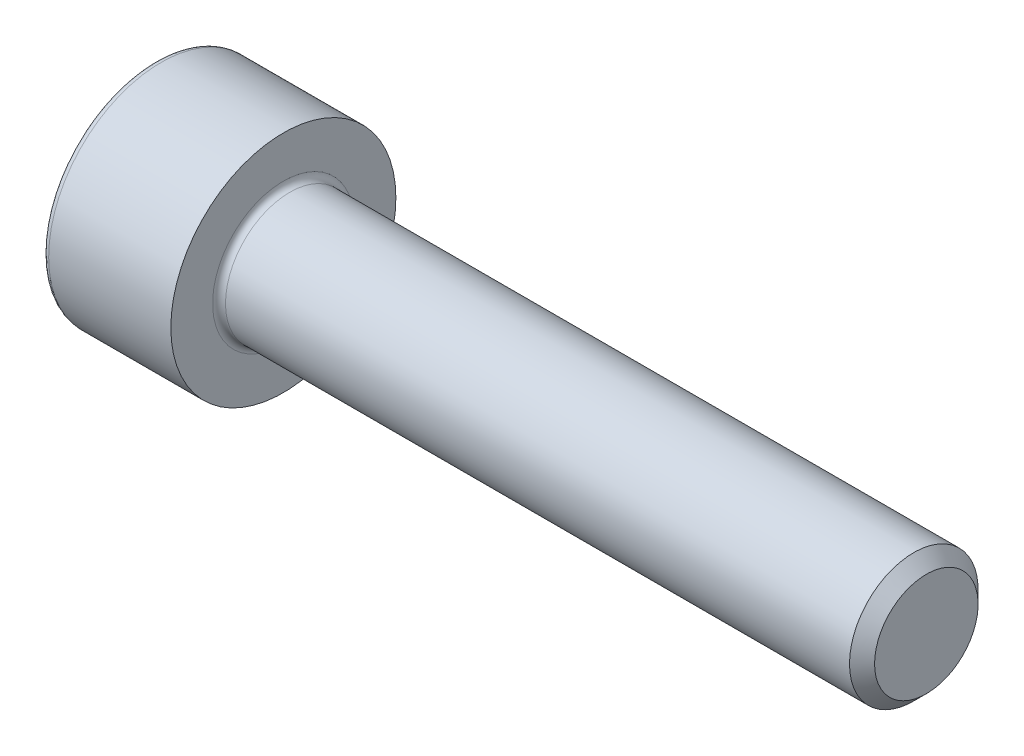
SolidWorks part; units mm, degrees
revolve "Base-Revolve" add sketch "BodySke"
sketch "BodySke" plane through (0, 0, 0) normal (0, 0, 1) x (1, 0, 0)
  line L0 (0, 0) -> (0, 3.5)
  line L1 (0, 3.5) -> (4, 3.5)
  line L2 (4, 3.5) -> (4, 2)
  line L3 (4, 2) -> (23.61, 2)
  line L4 (24, 1.61) -> (24, 0)
  line L5 (24, 0) -> (0, 0)
  line L6 (-31.75, 0) -> (127, 0) construction
  line L8 (24, 1.61) -> (23.61, 2)
  line L10 (24, -1.61) -> (23.61, -2) construction
  line L11 (4.7, 9.525) -> (4.7, 3.175) construction
  line L12 (18, 9.525) -> (18, 3.175) construction
  line L13 (-36, 9.525) -> (-36, 3.175) construction
  dimension "Head_ht" = 4
  dimension "Length" = 20
  dimension "Body_ch_ang" = 45
  dimension "Diameter" = 4
  dimension "Minor_dia" = 3.22
  dimension "Advance" = 0.7
  dimension "Thread_nom" = 6
  dimension "Thread_length" = 60
  dimension "Head_dia" = 7
cosmetic thread "ThreadCosmetic" [suppressed]
fillet "Fillet1" radius 0.2 1 edges at (4, 0, 2)
fillet "Fillet2" radius 0.2 1 edges at (0, 0, 3.5)
ref_plane "Plane1" through (0, 0, 0) normal (0, 0, 1) x (1, 0, 0)
ref_plane "Plane2" through (0, 0, 0) normal (0, 1, 0) x (1, 0, 0)
ref_plane "Plane3" through (0, 0, 0) normal (1, 0, 0) x (0, 0, -1)
sketch "Sketch2" plane through (0, 0, 0) normal (0, 0, 1) x (1, 0, 0)
  line L0 (0, 1.5355) -> (2, 1.5355)
  line L1 (2, 1.5355) -> (2.8865, 0)
  line L2 (-31.75, 0) -> (127, 0) construction
  line L3 (2.8865, 0) -> (0, 0)
  line L4 (0, 0) -> (0, 1.5355)
  line L6 (0, 0) -> (47.625, 0) construction
  dimension "D1" = 1.5355
  dimension "D2" = 60
  dimension "Depth" = 2
revolve "Hex-PreBroach" cut sketch "Sketch2" angle 360 about L6
sketch "Sketch3" plane through (0, 0, 0) normal (-1, 0, 0) x (0, 0.5, 0.866)
  line L0 (0.8865, 1.5355) -> (-0.8865, 1.5355)
  line L1 (-0.8865, 1.5355) -> (-1.773, 0)
  line L2 (0.8865, 1.5355) -> (1.773, 0)
  line L3 (0.8865, -1.5355) -> (1.773, 0)
  line L4 (0.8865, -1.5355) -> (-0.8865, -1.5355)
  line L5 (-0.8865, -1.5355) -> (-1.773, 0)
  dimension "D1" = 1.5355
  dimension "D2" = 1.5355
  dimension "Hex_size" = 3.071
extrude "Hex" cut sketch "Sketch3" against normal blind 2
sketch "ThdSchSke" plane through (0, 0, 0) normal (0, 0, 1) x (1, 0, 0)
  line L0 (18, -1.61) -> (17.7269, -2)
  line L1 (18, -1.61) -> (18.2731, -2)
  line L2 (18.2731, -2) -> (18.2731, -2.5)
  line L3 (-3.175, 0) -> (5.1513, 0) construction
  line L4 (0, 3.3) -> (0, -3.3) construction
  line L5 (18.2731, -2.5) -> (17.7269, -2.5)
  line L6 (17.7269, -2.5) -> (17.7269, -2)
  dimension "Thread_minor" = 3.22
  dimension "Diameter" = 4
  dimension "Start" = 18
revolve "ThreadSchematic" [suppressed] cut sketch "ThdSchSke" angle 360 about L3
pattern_linear "ThdSchPat" [suppressed]
equation "\"D2@Sketch3\" = \"Hex_size@Sketch3\" / 2"
equation "\"D1@Sketch3\" = \"Hex_size@Sketch3\" / 2"
equation "\"D1@Sketch2\" = \"Hex_size@Sketch3\" / 2"
equation "\"Thread_minor@ThreadCosmetic\"  =  \"Minor_dia@BodySke\""
equation "\"Depth@Sketch2\" =  \"Key_eng@Hex\""
equation "\"Thread_length@ThreadCosmetic\" = ((sgn( (\"Length@BodySke\" - \"Advance@BodySke\" * 3.0) - \"Thread_nom@BodySke\" )-1)*( (\"Length@BodySke\" - \"Advance@BodySke\" * 3.0) - \"Thread_nom@BodySke\" ))/-2+ \"Thread_nom@BodySke\""
equation "\"Thread_minor@ThdSchSke\" = \"Minor_dia@BodySke\""
equation "\"Diameter@ThdSchSke\" = \"Diameter@BodySke\""
equation "\"Overcut@ThdSchSke\" = \"Diameter@BodySke\" * 1.25"
equation "\"Start@ThdSchSke\" = \"Head_ht@BodySke\" + \"Length@BodySke\" - \"Thread_length@ThreadCosmetic\"  '---Non-countersunk---"
equation "\"Num_threads@ThdSchPat\" = int( \"Thread_length@ThreadCosmetic\" / \"Advance@BodySke\" + 0.999 )  + 1"
equation "\"Advance@ThdSchPat\" = \"Thread_length@ThreadCosmetic\" /  (\"Num_threads@ThdSchPat\" - 1) 'relax it"
equation "\"Num_threads@ThdSchPat\" = \"Num_threads@ThdSchPat\" - sgn( \"Num_threads@ThdSchPat\" - 1) '---chamfered tips only---"
